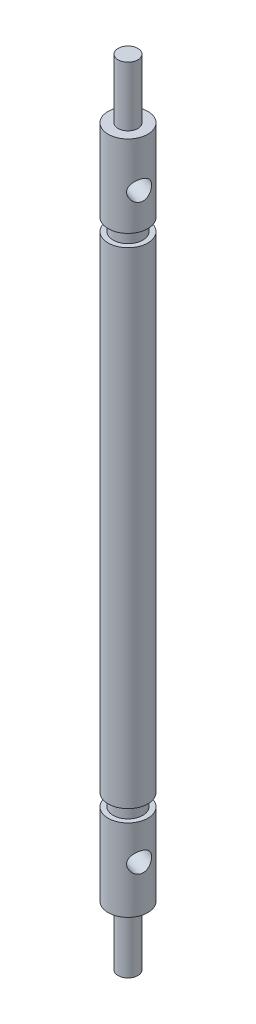
SolidWorks part; units mm, degrees
material "1023 Carbon Steel Sheet (SS)"
ref_plane "Front Plane" through (0, 0, 0) normal (0, 0, 1) x (1, 0, 0)
ref_plane "Top Plane" through (0, 0, 0) normal (0, 1, 0) x (1, 0, 0)
ref_plane "Right Plane" through (0, 0, 0) normal (1, 0, 0) x (0, 0, -1)
sketch "Sketch1" plane through (0, 0, 0) normal (1, 0, 0) x (0, 0, -1)
  line L0 (-1, 20) -> (1, -20) construction
  line L1 (-1, 20) -> (0, 20)
  line L2 (-1, 20) -> (-1, -20)
  line L3 (-1, -20) -> (1, -20)
  line L4 (1, 14) -> (1, 5.75)
  line L5 (0, 20) -> (0, 14)
  line L6 (0, 14) -> (1, 14)
  line L7 (1, 5.75) -> (0.5, 5.75)
  line L8 (0.5, 5.75) -> (0.5, 4.5)
  line L9 (0.5, 4.5) -> (1, 4.5)
  line L10 (1, 4.5) -> (1, -20)
  dimension "D1" = 40
  dimension "D2" = 2
  dimension "D3" = 6
  dimension "D4" = 8.25
  dimension "D5" = 0.5
  dimension "D6" = 1.25
revolve "Revolve1" add sketch "Sketch1" angle 360 about L2
hole_wizard "Ø2.0mm Press Dowel Hole1" positions "3DSketch1" profile "Sketch2" hole size "Ø2.0" standard "JIS" end condition through all
sketch3d "3DSketch1"
  point P0 (1.904, 9.34, 1.6122)
  dimension "D1" = 10.66
sketch "Sketch2" plane through (1.904, 9.34, 1.6122) normal (0, 1, 0) x (0.3061, 0, -0.952)
  line L0 (0, 0) -> (0, 4.5162)
  line L1 (0, 4.5162) -> (1.0025, 4.5162)
  line L2 (1.0025, 4.5162) -> (1.0025, 0)
  line L5 (1.0025, 0) -> (0, 0)
  line L11 (0, -6.35) -> (0, 107.95) construction
  dimension "Thru Hole Dia." = 2.005
  dimension "Thru Hole Depth" = 4.5162
mirror "Mirror1" about plane through (0, -20, 1) normal (0, 1, 0) of "Ø2.0mm Press Dowel Hole1", "Revolve1"
